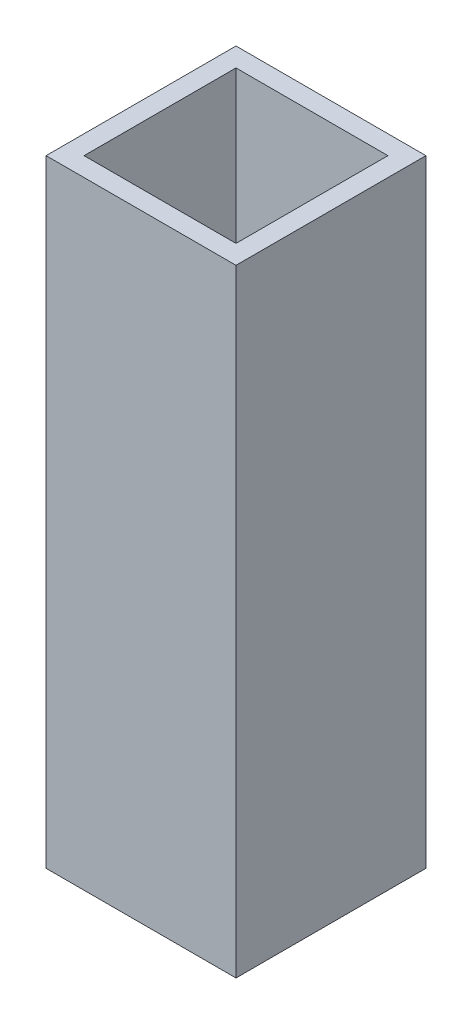
SolidWorks part; units mm, degrees
ref_plane "Front Plane" through (0, 0, 0) normal (0, 0, 1) x (1, 0, 0)
ref_plane "Top Plane" through (0, 0, 0) normal (0, 1, 0) x (1, 0, 0)
ref_plane "Right Plane" through (0, 0, 0) normal (1, 0, 0) x (0, 0, -1)
sketch "Sketch1" plane through (0, 0, 0) normal (0, 1, 0) x (1, 0, 0)
  line L1 (0, 0) -> (25.4, 0)
  line L2 (0, 0) -> (0, 25.4)
  line L3 (0, 25.4) -> (25.4, 25.4)
  line L4 (25.4, 0) -> (25.4, 25.4)
  dimension "D1" = 25.4
  dimension "D2" = 25.4
extrude "Extrude-Thin1" add sketch "Sketch1" along normal blind 82.55 thin thin type one direction reverse wall 2.54
